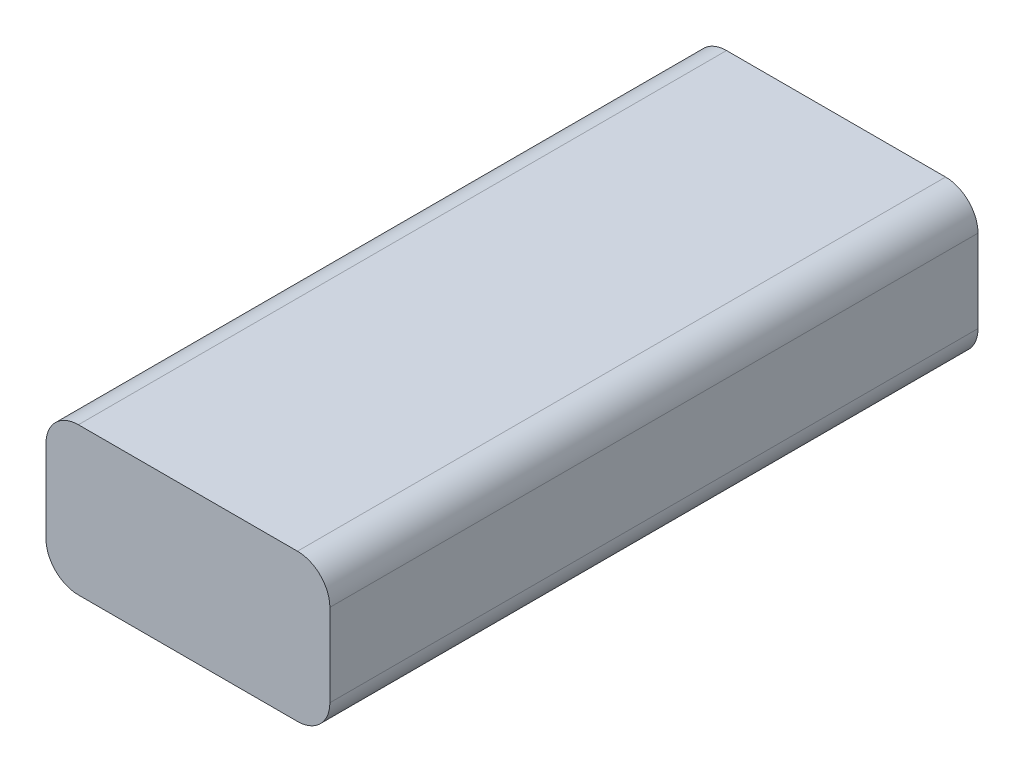
SolidWorks part; units mm, degrees
ref_plane "Front Plane" through (0, 0, 0) normal (0, 0, 1) x (1, 0, 0)
ref_plane "Top Plane" through (0, 0, 0) normal (0, 1, 0) x (1, 0, 0)
ref_plane "Right Plane" through (0, 0, 0) normal (1, 0, 0) x (0, 0, -1)
sketch "Sketch1" plane through (0, 0, 0) normal (0, 0, 1) x (1, 0, 0)
  line L0 (-3.267, 4.2026) -> (5.3182, 4.2026)
  line L1 (6.5882, 2.9326) -> (6.5882, -0.3059)
  line L2 (5.3182, -1.5759) -> (-3.267, -1.5759)
  line L3 (-4.537, -0.3059) -> (-4.537, 2.9326)
  arc A0 (-4.537, -0.3059) -> (-3.267, -1.5759) centre (-3.267, -0.3059) ccw
  arc A1 (5.3182, -1.5759) -> (6.5882, -0.3059) centre (5.3182, -0.3059) ccw
  arc A2 (6.5882, 2.9326) -> (5.3182, 4.2026) centre (5.3182, 2.9326) ccw
  arc A3 (-3.267, 4.2026) -> (-4.537, 2.9326) centre (-3.267, 2.9326) ccw
  point P8 (6.5882, -1.5759)
  point P11 (6.5882, 4.2026)
  point P14 (-4.537, 4.2026)
  dimension "D3" = 1.27
  dimension "D1" = 11.1252
  dimension "D2" = 5.7785
extrude "Boss-Extrude1" add sketch "Sketch1" along normal blind 25.4
